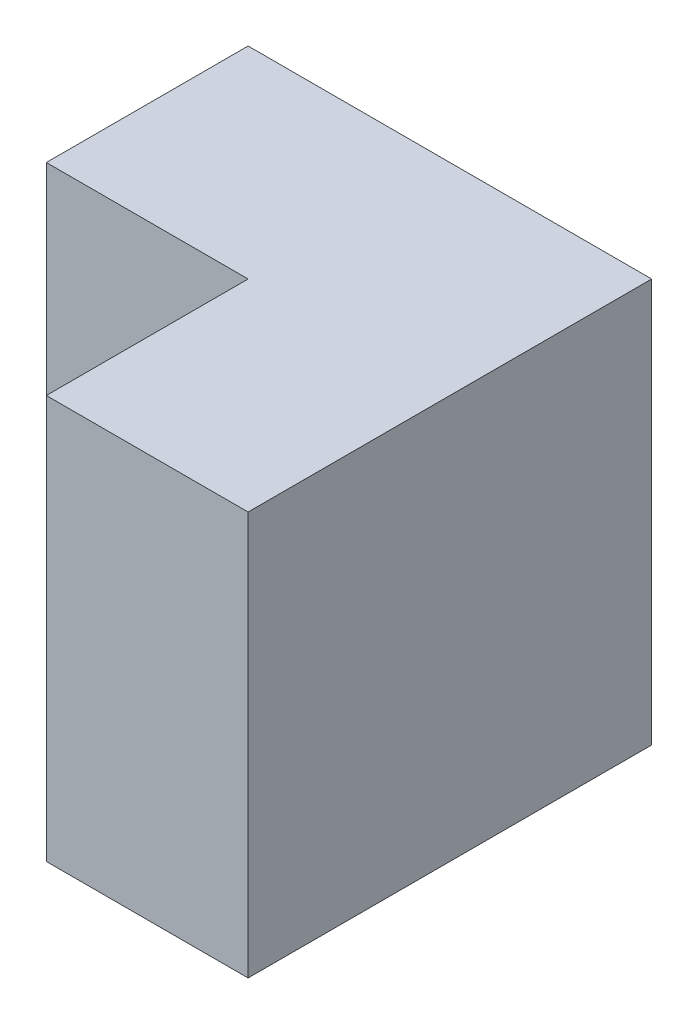
SolidWorks part; units mm, degrees
ref_plane "Front Plane" through (0, 0, 0) normal (0, 0, 1) x (1, 0, 0)
ref_plane "Top Plane" through (0, 0, 0) normal (0, 1, 0) x (1, 0, 0)
ref_plane "Right Plane" through (0, 0, 0) normal (1, 0, 0) x (0, 0, -1)
sketch "Sketch3" plane through (0, 0, 0) normal (0, 0, 1) x (1, 0, 0)
  line L1 (0, 0) -> (20, 0)
  line L2 (0, 0) -> (0, 20)
  line L3 (0, 20) -> (20, 20)
  line L4 (20, 0) -> (20, 20)
  dimension "D1" = 20
  dimension "D2" = 20
extrude "Boss-Extrude1" add sketch "Sketch3" along normal blind 20
sketch "Sketch4" plane through (0, 0, 20) normal (0, 0, 1) x (1, 0, 0)
  line L0 (0, 0) -> (20, 0) construction
  line L1 (0, 20) -> (10, 20)
  line L2 (0, 20) -> (0, 0)
  line L3 (0, 0) -> (10, 0)
  line L4 (10, 20) -> (10, 0)
  dimension "D1" = 10
extrude "Cut-Extrude1" cut sketch "Sketch4" against normal blind 10
